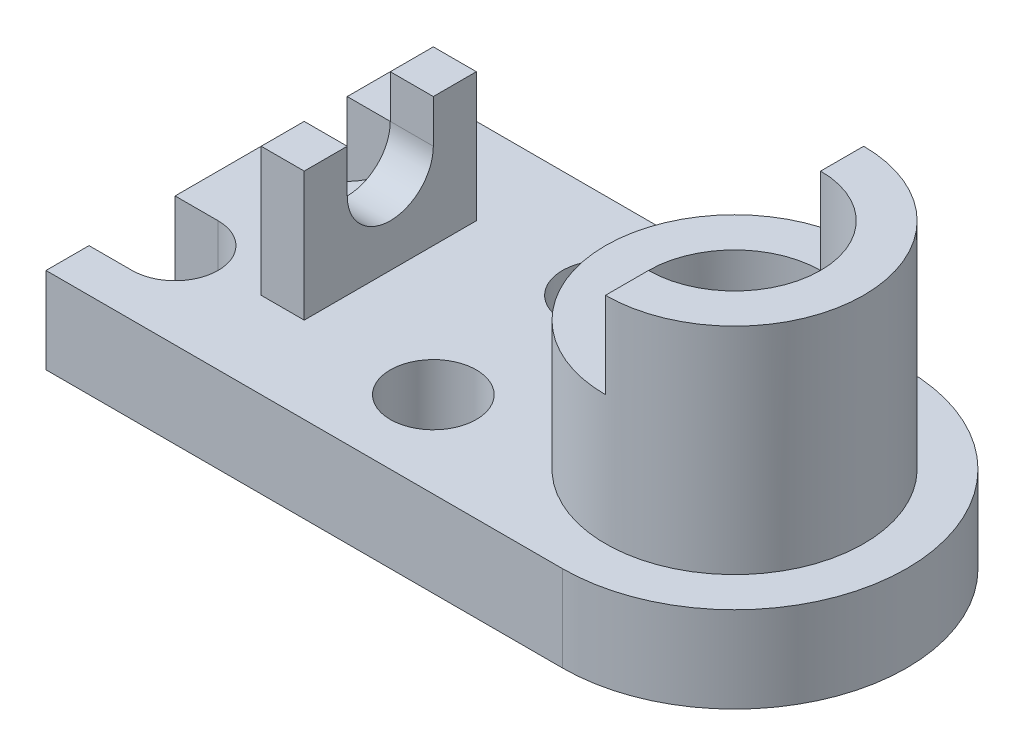
SolidWorks part; units mm, degrees
ref_plane "Front Plane" through (0, 0, 0) normal (0, 0, 1) x (1, 0, 0)
ref_plane "Top Plane" through (0, 0, 0) normal (0, 1, 0) x (1, 0, 0)
ref_plane "Right Plane" through (0, 0, 0) normal (1, 0, 0) x (0, 0, -1)
sketch "Sketch2" plane through (0, 0, 0) normal (0, 1, 0) x (1, 0, 0)
  line L0 (0, 40) -> (0, -40)
  line L1 (0, -40) -> (120, -40)
  line L2 (0, 40) -> (120, 40)
  arc A0 (120, 40) -> (120, -40) centre (120, 0) cw
  dimension "D2" = 40
  dimension "D5" = 40
  dimension "D1" = 80
  dimension "D3" = 120
  dimension "D4" = 120
extrude "Boss-Extrude1" add sketch "Sketch2" along normal blind 20
sketch "Sketch3" plane through (0, 20, 0) normal (0, 1, 0) x (1, 0, 0)
  line L0 (0, 30) -> (10, 30)
  line L1 (0, 40) -> (0, -40) construction
  line L2 (0, 10) -> (10, 10)
  line L3 (0, -10) -> (10, -10)
  line L4 (0, -30) -> (10, -30)
  line L5 (0, -10) -> (0, -30)
  line L6 (0, 10) -> (0, 30)
  arc A0 (10, 30) -> (10, 10) centre (10, 20) cw
  arc A1 (10, -10) -> (10, -30) centre (10, -20) cw
  dimension "D1" = 10
  dimension "D8" = 10
  dimension "D2" = 10
  dimension "D3" = 10
  dimension "D4" = 20
  dimension "D5" = 10
  dimension "D6" = 10
  dimension "D7" = 20
  dimension "D9" = 10
extrude "Cut-Extrude1" cut sketch "Sketch3" against normal blind 20
sketch "Sketch4" plane through (0, 20, 0) normal (0, 1, 0) x (1, 0, 0)
  line L0 (120, 40) -> (0, 40) construction
  line L1 (0, -40) -> (120, -40) construction
  circle A0 centre (70, 20) radius 10
  circle A1 centre (70, -20) radius 10
  dimension "D1" = 20
  dimension "D2" = 20
  dimension "D3" = 20
  dimension "D4" = 20
  dimension "D5" = 70
  dimension "D6" = 70
extrude "Cut-Extrude2" cut sketch "Sketch4" against normal blind 20
sketch "Sketch5" plane through (0, 20, 0) normal (0, 1, 0) x (1, 0, 0)
  circle A0 centre (120, 0) radius 20
  arc A1 (120, -40) -> (120, 40) centre (120, 0) ccw construction
  point P2 (160, 0)
  dimension "D1" = 40
  dimension "D2" = 40
  dimension "D3" = 40
extrude "Boss-Extrude2" add sketch "Sketch5" along normal blind 20
sketch "Sketch6" plane through (0, 20, 0) normal (0, 1, 0) x (1, 0, 0)
  circle A0 centre (120, 0) radius 30
  dimension "D1" = 60
extrude "Boss-Extrude3" add sketch "Sketch6" along normal blind 30
sketch "Sketch7" plane through (0, 50, 0) normal (0, 1, 0) x (1, 0, 0)
  circle A0 centre (120, 0) radius 20
  dimension "D1" = 40
extrude "Cut-Extrude3" cut sketch "Sketch7" against normal blind 10
sketch "Sketch8" plane through (0, 40, 0) normal (0, 1, 0) x (1, 0, 0)
  circle A0 centre (120, 0) radius 10
  dimension "D1" = 20
extrude "Cut-Extrude4" cut sketch "Sketch8" against normal blind 72
sketch "Sketch9" plane through (0, 50, 0) normal (0, 1, 0) x (1, 0, 0)
  line L0 (120, 20) -> (120, 30)
  line L1 (120, -20) -> (120, -30)
  circle A0 centre (120, 0) radius 20 construction
  circle A1 centre (120, 0) radius 30 construction
  arc A2 (120, 30) -> (120, -30) centre (120, 0) cw
  arc A3 (120, 20) -> (120, -20) centre (120, 0) cw
  dimension "D1" = 10
extrude "Boss-Extrude4" add sketch "Sketch9" along normal blind 20
sketch "Sketch10" plane through (0, 20, 0) normal (0, 1, 0) x (1, 0, 0)
  line L1 (40, 20) -> (30, 20)
  line L2 (40, 20) -> (40, -20)
  line L3 (40, -20) -> (30, -20)
  line L4 (30, 20) -> (30, -20)
  dimension "D1" = 10
  dimension "D2" = 40
  dimension "D3" = 20
  dimension "D4" = 30
extrude "Boss-Extrude5" add sketch "Sketch10" along normal blind 30
sketch "Sketch11" plane through (30, 0, 0) normal (-1, 0, 0) x (0, 0, 1)
  line L0 (-10, 50) -> (-10, 40)
  line L1 (-20, 50) -> (20, 50) construction
  line L2 (10, 50) -> (10, 40)
  line L3 (-10, 50) -> (10, 50)
  arc A0 (-10, 40) -> (10, 40) centre (0, 40) ccw
  dimension "D1" = 10
  dimension "D2" = 10
  dimension "D3" = 10
  dimension "D4" = 10
  dimension "D5" = 10
extrude "Cut-Extrude5" cut sketch "Sketch11" against normal blind 30
